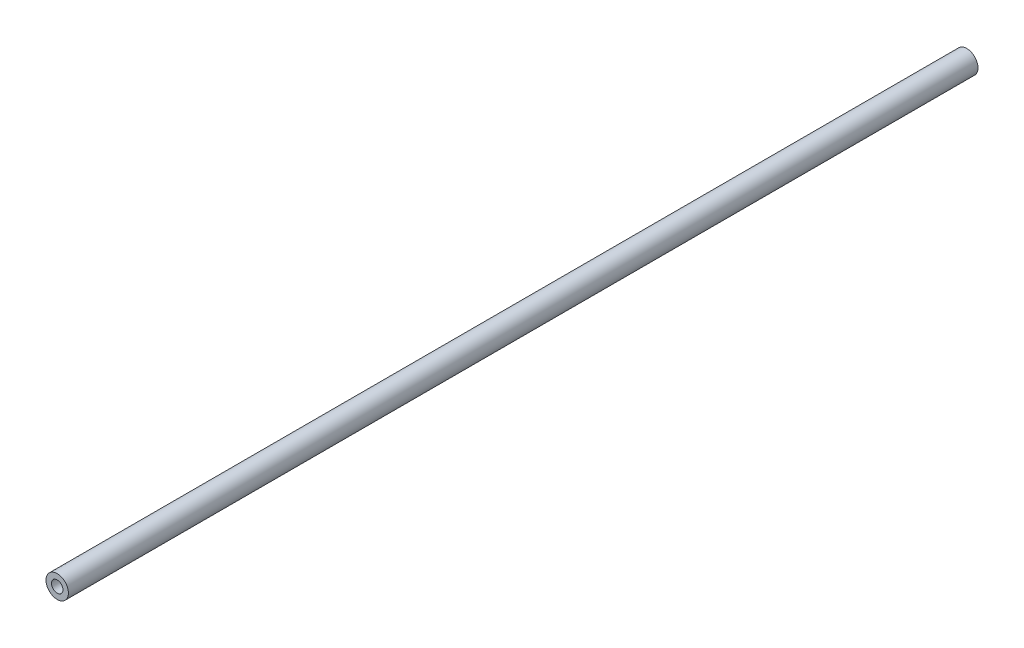
SolidWorks part; units mm, degrees
ref_plane "Alzado" through (0, 0, 0) normal (0, 0, 1) x (1, 0, 0)
ref_plane "Planta" through (0, 0, 0) normal (0, 1, 0) x (1, 0, 0)
ref_plane "Vista lateral" through (0, 0, 0) normal (1, 0, 0) x (0, 0, -1)
sketch "Croquis1" plane through (0, 0, 0) normal (0, 0, 1) x (1, 0, 0)
  circle A0 centre (0, 0) radius 1.85
  circle A1 centre (0, 0) radius 0.95
  dimension "D1" = 3.7
  dimension "D2" = 1.9
extrude "Saliente-Extruir1" add sketch "Croquis1" along normal blind 150
